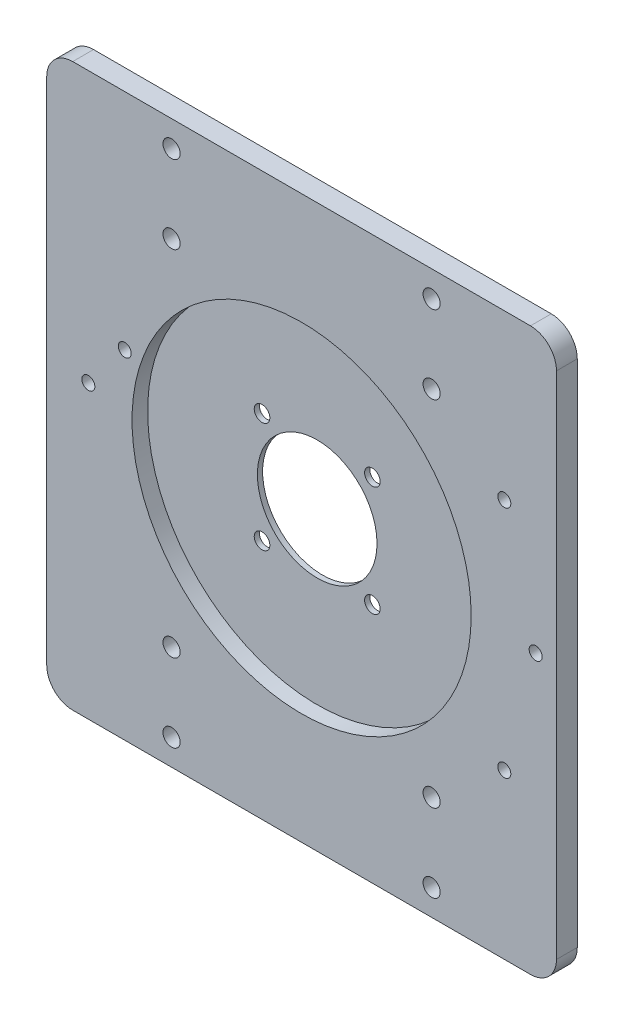
SolidWorks part; units mm, degrees
ref_plane "前视基准面" through (0, 0, 0) normal (0, 0, 1) x (1, 0, 0)
ref_plane "上视基准面" through (0, 0, 0) normal (0, 1, 0) x (1, 0, 0)
ref_plane "右视基准面" through (0, 0, 0) normal (1, 0, 0) x (0, 0, -1)
sketch "草图1" plane through (0, 0, 0) normal (0, 0, 1) x (1, 0, 0)
  line L1 (49, -54) -> (-49, -54)
  line L2 (49, -54) -> (49, 54)
  line L3 (49, 54) -> (-49, 54)
  line L4 (-49, -54) -> (-49, 54)
  line L5 (49, -54) -> (-49, 54) construction
  line L6 (49, 54) -> (-49, -54) construction
  point P0 (0, 0)
  dimension "D1" = 108
  dimension "D2" = 98
extrude "凸台-拉伸1" add sketch "草图1" along normal blind 4
sketch "草图2" plane through (0, 0, 4) normal (0, 0, 1) x (1, 0, 0)
  circle A0 centre (0, 0) radius 11.5
  dimension "D1" = 23
extrude "切除-拉伸1" cut sketch "草图2" against normal blind 10
sketch "草图3" plane through (0, 0, 4) normal (0, 0, 1) x (1, 0, 0)
  circle A0 centre (0, 0) radius 32.6
  dimension "D1" = 65.2
extrude "切除-拉伸2" cut sketch "草图3" against normal blind 3
sketch "草图4" plane through (0, 0, 1) normal (0, 0, 1) x (1, 0, 0)
  line L0 (0, 0) -> (0, 28.3357) construction
  line L1 (0, 0) -> (-19.4858, 19.4858) construction
  line L2 (0, 0) -> (15.4493, -15.4493) construction
  line L3 (0, 0) -> (17.4757, 17.4757) construction
  line L4 (0, 0) -> (-16.2019, -16.2019) construction
  circle A0 centre (0, 0) radius 15 construction
  circle A1 centre (-10.6066, 10.6066) radius 1.5
  circle A2 centre (10.6066, -10.6066) radius 1.5
  circle A3 centre (10.6066, 10.6066) radius 1.5
  circle A4 centre (-10.6066, -10.6066) radius 1.5
  point P16 (1.2784, 2.576)
  dimension "D1" = 30
  dimension "D2" = 3
  dimension "D5" = 3
  dimension "D7" = 3
  dimension "D9" = 3
  dimension "D4" = 45
  dimension "D3" = 135
  dimension "D6" = 45
  dimension "D8" = 90
extrude "切除-拉伸3" cut sketch "草图4" against normal blind 2
fillet "圆角1" radius 5 4 edges at (-49, -54, 2) (49, -54, 2) (49, 54, 2) (-49, 54, 2)
hole_wizard "M4 螺纹孔1" positions "草图5" profile "草图6" tap size "M4" standard "GB"
sketch "草图5" plane through (0, 0, 0) normal (0, 0, -1) x (-1, 0, 0)
  point P0 (-25, 49)
  point P2 (-25, 34)
  point P4 (25, 34)
  point P6 (25, 49)
  point P8 (-25, -34)
  point P10 (-25, -49)
  point P12 (25, -49)
  point P14 (25, -34)
sketch "草图6" plane through (25, 49, 0) normal (1, 0, 0) x (0, 1, 0)
  line L0 (0, 0) -> (0, 11.0914)
  line L1 (0, 11.0914) -> (1.65, 10.1)
  line L2 (1.65, 10.1) -> (1.65, 0)
  line L5 (1.65, 0) -> (0, 0)
  line L10 (0, 11.0914) -> (-1.65, 10.1) construction
  line L11 (0, -6.35) -> (0, 107.95) construction
  dimension "螺纹孔钻头直径" = 3.3
  dimension "螺纹孔钻头深度" = 10.1
  dimension "导头角度" = 118
cosmetic thread "孔螺蚊线1" parameters "D1"=4, "D2"=4
cosmetic thread "孔螺蚊线2" parameters "D1"=4, "D2"=4
cosmetic thread "孔螺蚊线3" parameters "D1"=4, "D2"=4
cosmetic thread "孔螺蚊线4" parameters "D1"=4, "D2"=4
cosmetic thread "孔螺蚊线5" parameters "D1"=4, "D2"=4
cosmetic thread "孔螺蚊线6" parameters "D1"=4, "D2"=4
cosmetic thread "孔螺蚊线7" parameters "D1"=4, "D2"=4
cosmetic thread "孔螺蚊线8" parameters "D1"=4, "D2"=4
hole_wizard "M3 螺纹孔1" positions "草图7" profile "草图8" tap size "M3" standard "GB"
sketch "草图7" plane through (0, 0, 0) normal (0, 0, -1) x (-1, 0, 0)
  point P2 (41, 2)
  point P4 (34, 11)
sketch "草图8" plane through (-41, 2, 0) normal (1, 0, 0) x (0, 1, 0)
  line L0 (0, 0) -> (0, 8.2511)
  line L1 (0, 8.2511) -> (1.25, 7.5)
  line L2 (1.25, 7.5) -> (1.25, 0)
  line L5 (1.25, 0) -> (0, 0)
  line L10 (0, 8.2511) -> (-1.25, 7.5) construction
  line L11 (0, -6.35) -> (0, 107.95) construction
  dimension "螺纹孔钻头直径" = 2.5
  dimension "螺纹孔钻头深度" = 7.5
  dimension "导头角度" = 118
cosmetic thread "孔螺蚊线9" parameters "D1"=4, "D2"=3
cosmetic thread "孔螺蚊线10" parameters "D1"=4, "D2"=3
hole_wizard "M3 螺纹孔2" positions "草图9" profile "草图10" tap size "M3" standard "GB"
sketch "草图9" plane through (0, 0, 4) normal (0, 0, 1) x (1, 0, 0)
  line L0 (0, 0) -> (66.473, 0) construction
  line L2 (0, 0) -> (77.186, 44.5633) construction
  line L4 (0, 0) -> (65.1403, -37.6088) construction
  circle A0 centre (0, 0) radius 45
  point P0 (38.9711, 22.5)
  point P2 (45, 0)
  point P4 (38.9711, -22.5)
  dimension "D3" = 90
  dimension "D1" = 30
  dimension "D2" = 30
sketch "草图10" plane through (38.9711, 22.5, 4) normal (1, 0, 0) x (0, -1, 0)
  line L0 (0, 0) -> (0, 8.2511)
  line L1 (0, 8.2511) -> (1.25, 7.5)
  line L2 (1.25, 7.5) -> (1.25, 0)
  line L5 (1.25, 0) -> (0, 0)
  line L10 (0, 8.2511) -> (-1.25, 7.5) construction
  line L11 (0, -6.35) -> (0, 107.95) construction
  dimension "螺纹孔钻头直径" = 2.5
  dimension "螺纹孔钻头深度" = 7.5
  dimension "导头角度" = 118
cosmetic thread "孔螺蚊线11" parameters "D1"=4, "D2"=3
cosmetic thread "孔螺蚊线12" parameters "D1"=4, "D2"=3
cosmetic thread "孔螺蚊线13" parameters "D1"=4, "D2"=3
